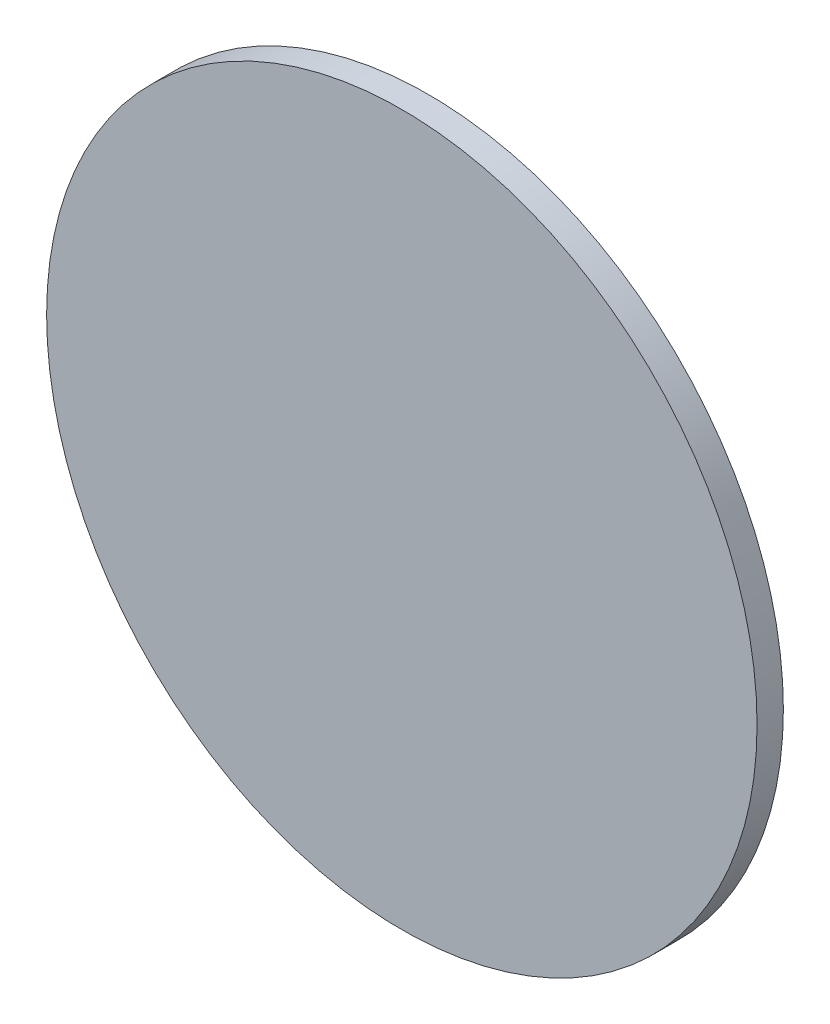
SolidWorks part; units mm, degrees
ref_plane "Front Plane" through (0, 0, 0) normal (0, 0, 1) x (1, 0, 0)
ref_plane "Top Plane" through (0, 0, 0) normal (0, 1, 0) x (1, 0, 0)
ref_plane "Right Plane" through (0, 0, 0) normal (1, 0, 0) x (0, 0, -1)
sketch "Sketch1" plane through (0, 0, 0) normal (0, 0, 1) x (1, 0, 0)
  circle A0 centre (0, 0) radius 27
  dimension "D1" = 54
extrude "Boss-Extrude1" add sketch "Sketch1" along normal blind 2
